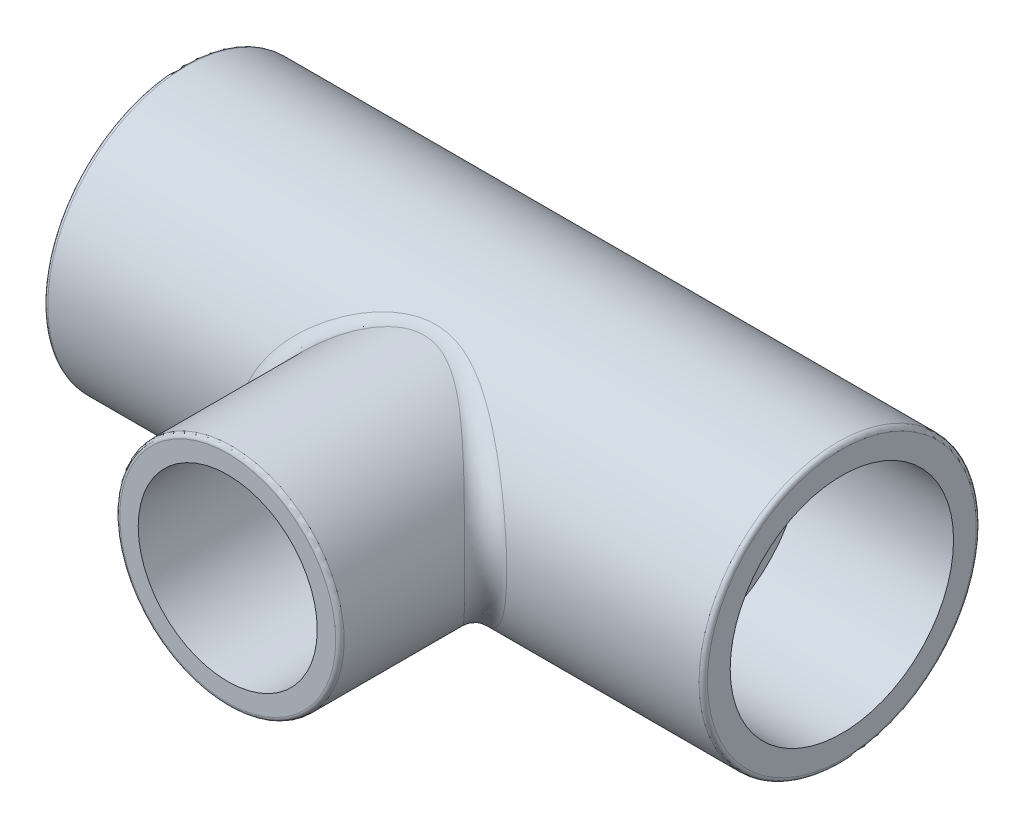
SolidWorks part; units mm, degrees
ref_plane "Front Plane" through (0, 0, 0) normal (1, 0, 0) x (0, 1, 0)
ref_plane "Top Plane" through (0, 0, 0) normal (0, 0, 1) x (0, 1, 0)
ref_plane "Right Plane" through (0, 0, 0) normal (0, 1, 0) x (-1, 0, 0)
sketch "Sketch1" plane through (0, 0, 0) normal (1, 0, 0) x (0, 1, 0)
  circle A0 centre (0, 0) radius 0.6565
  circle A1 centre (0, 0) radius 0.412
  dimension "D1" = 1.313
  dimension "D2" = 0.824
extrude "Boss-Extrude1" add sketch "Sketch1" along normal blind 3.125
sketch "Sketch2" plane through (3.125, 0, 0) normal (1, 0, 0) x (0, 0, -1)
  circle A0 centre (0, 0) radius 0.529
  dimension "D1" = 1.058
extrude "Cut-Extrude1" cut sketch "Sketch2" against normal blind 0.72
sketch "Sketch3" plane through (0, 0, 0) normal (-1, 0, 0) x (0, 0, 1)
  circle A0 centre (0, 0) radius 0.529
  dimension "D1" = 1.058
extrude "Cut-Extrude2" cut sketch "Sketch3" against normal blind 0.72
sketch "Sketch4" plane through (0, 0, 0) normal (0, 0, 1) x (0, 1, 0)
  line L0 (0, 0) -> (0, -3.125) construction
  line L1 (-0.6565, -3.125) -> (0.6565, -3.125) construction
  line L2 (-0.6565, -1.5625) -> (0.6565, -1.5625) construction
  line L3 (-0.6565, 0) -> (-0.6565, -3.125) construction
  line L4 (0.6565, -3.125) -> (0.6565, 0) construction
  circle A0 centre (0, -1.5625) radius 0.5315
  circle A1 centre (0, -1.5625) radius 0.311
  dimension "D1" = 1.063
  dimension "D2" = 0.622
extrude "Boss-Extrude2" add sketch "Sketch4" along normal blind 1.3465
sketch "Sketch5" plane through (3.125, 0, 0) normal (1, 0, 0) x (0, 1, 0)
  circle A0 centre (0, 0) radius 0.412
  dimension "D1" = 0.824
extrude "Cut-Extrude3" cut sketch "Sketch5" against normal through all
sketch "Sketch6" plane through (0, 0, 1.3465) normal (0, 0, 1) x (1, 0, 0)
  circle A0 centre (1.5625, 0) radius 0.311
  dimension "D1" = 0.622
extrude "Cut-Extrude4" cut sketch "Sketch6" against normal up to next
sketch "Sketch8" plane through (0, 0, 1.3465) normal (0, 0, 1) x (1, 0, 0)
  circle A0 centre (1.5625, 0) radius 0.424
  dimension "D1" = 0.848
extrude "Cut-Extrude5" cut sketch "Sketch8" against normal blind 0.69
fillet "Fillet1" radius 0.1 1 edges at (1.0335, -0.0518, 0.6545)
fillet "Fillet2" radius 0.02 1 edges at (2.094, 0, 1.3465)
fillet "Fillet3" radius 0.02 1 edges at (0, 0, -0.6565)
fillet "Fillet4" radius 0.02 1 edges at (3.125, 0, -0.6565)
